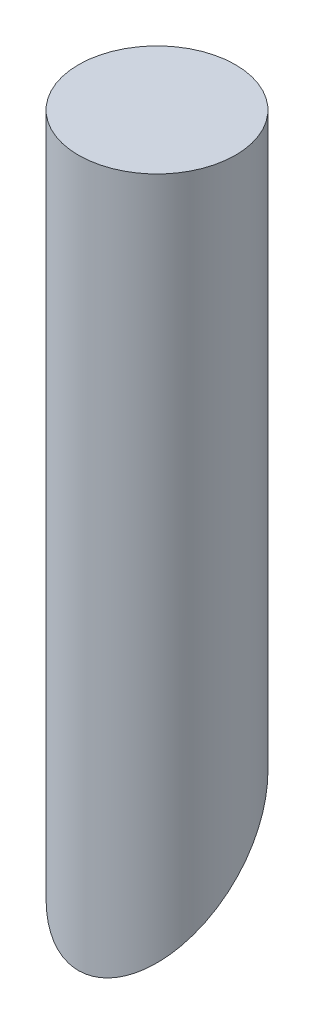
SolidWorks part; units mm, degrees
ref_plane "Front Plane" through (0, 0, 0) normal (0, 0, 1) x (1, 0, 0)
ref_plane "Top Plane" through (0, 0, 0) normal (0, 1, 0) x (1, 0, 0)
ref_plane "Right Plane" through (0, 0, 0) normal (1, 0, 0) x (0, 0, -1)
sketch "Sketch1" plane through (0, 0, 0) normal (0, 1, 0) x (1, 0, 0)
  circle A0 centre (0, 0) radius 31.75
  dimension "D1" = 63.5
extrude "Boss-Extrude1" add sketch "Sketch1" along normal blind 222.25
sketch "Sketch2" plane through (0, 0, 0) normal (0, -1, 0) x (1, 0, 0)
  circle A0 centre (0, 0) radius 31.75
  dimension "D1" = 63.5
extrude "Boss-Extrude2" add sketch "Sketch2" along normal blind 63.5
ref_plane "Plane1" through (31.75, 0, 0) normal (1, 0, 0) x (0, 0, -1)
sketch "Sketch3" plane through (31.75, 0, 0) normal (1, 0, 0) x (0, 0, -1)
  line L0 (-31.75, 0) -> (31.75, 0)
  line L1 (31.75, 0) -> (-31.75, 0) construction
  line L2 (31.75, 0) -> (31.75, -63.5)
  line L3 (31.75, -63.5) -> (-31.75, -63.5)
  line L4 (-31.75, -63.5) -> (31.75, -63.5) construction
  line L5 (-31.75, -63.5) -> (-31.75, 0)
  line L6 (31.75, 0) -> (-31.75, -63.5)
extrude "Cut-Extrude1" cut sketch "Sketch3" against normal blind 63.5 contours L2 L6 L3
equation "\"FrontNoodle\"= ( \"length desired@Drivetrain.Assembly\" / 2 ) - ( \"CutOutLength\" / 2 ) + 0.75"
equation "\"CutOutLength\"= \"LengthOfCutOut@Drivetrain.Assembly\""
equation "\"D1@Boss-Extrude1\"=\"FrontNoodle\""
